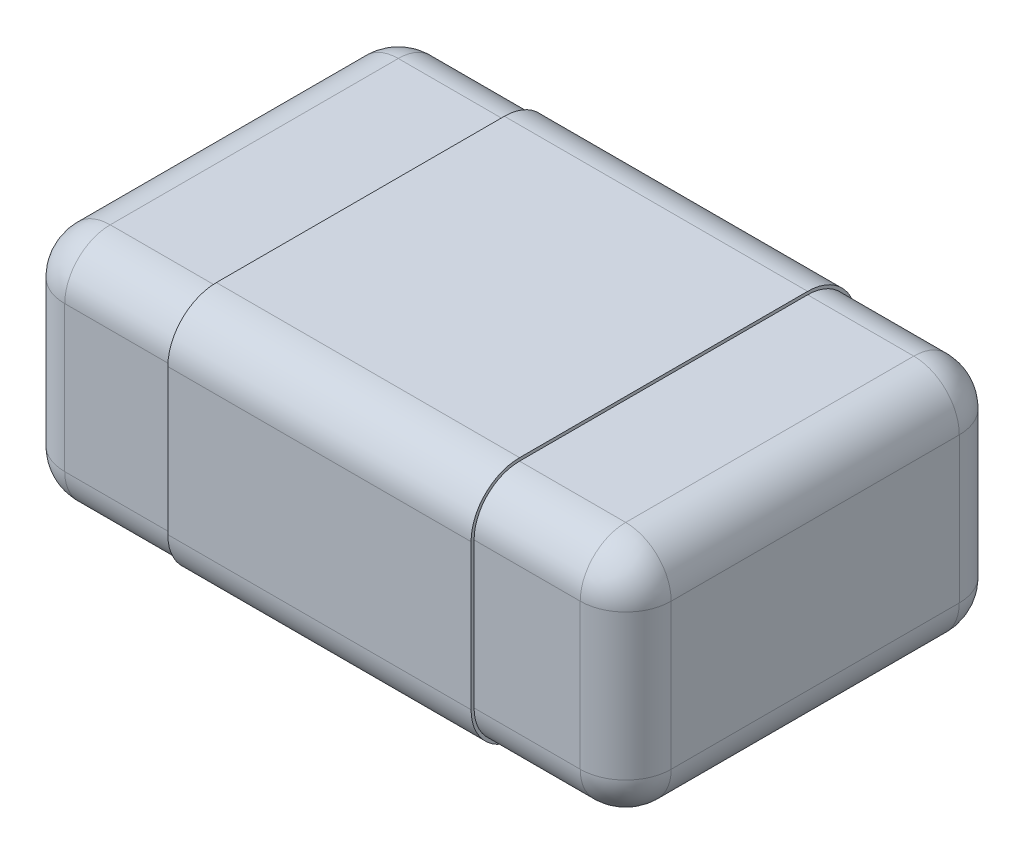
SolidWorks part; units mm, degrees
material "Aço inoxidável fundido"
ref_plane "Plano frontal" through (0, 0, 0) normal (0, 0, 1) x (1, 0, 0)
ref_plane "Plano superior" through (0, 0, 0) normal (0, 1, 0) x (1, 0, 0)
ref_plane "Plano direito" through (0, 0, 0) normal (1, 0, 0) x (0, 0, -1)
sketch "Esboço1" plane through (0, 0, 0) normal (0, 1, 0) x (1, 0, 0)
  line L0 (-1, -0.625) -> (1, -0.625)
  line L1 (1, -0.625) -> (1, 0.625)
  line L2 (1, 0.625) -> (-1, 0.625)
  line L3 (-1, 0.625) -> (-1, -0.625)
extrude "Ressalto-extrusão1" add sketch "Esboço1" against normal blind 0.78
fillet "Filete1" radius 0.15 12 edges at (0, -0.78, -0.625) (-1, -0.39, -0.625) (1, -0.39, -0.625) (0, 0, -0.625) (-1, -0.78, 0) (1, -0.78, 0) (0, -0.78, 0.625) (-1, 0, 0) (1, 0, 0) (-1, -0.39, 0.625) (1, -0.39, 0.625) (0, 0, 0.625)
sketch "Esboço4" plane through (0, 0, 0) normal (1, 0, 0) x (0, 0, -1)
  line L0 (0.625, -0.63) -> (0.625, -0.15) construction
  line L1 (0.625, -0.63) -> (0.625, -0.15)
  line L2 (0.475, -0.78) -> (-0.475, -0.78) construction
  line L3 (0.475, -0.78) -> (-0.475, -0.78)
  line L4 (0.475, 0) -> (-0.475, 0) construction
  line L5 (-0.625, -0.15) -> (-0.625, -0.63) construction
  line L6 (0.475, 0) -> (-0.475, 0)
  line L7 (-0.625, -0.15) -> (-0.625, -0.63)
  line L8 (0.635, -0.63) -> (0.635, -0.15)
  line L9 (0.475, 0.01) -> (-0.475, 0.01)
  line L10 (-0.635, -0.15) -> (-0.635, -0.63)
  line L11 (0.475, -0.79) -> (-0.475, -0.79)
  arc A5 (0.475, -0.78) -> (0.625, -0.63) centre (0.475, -0.63) ccw construction
  arc A6 (0.475, -0.78) -> (0.625, -0.63) centre (0.475, -0.63) ccw
  arc A7 (-0.475, 0) -> (-0.625, -0.15) centre (-0.475, -0.15) ccw construction
  arc A8 (-0.625, -0.63) -> (-0.475, -0.78) centre (-0.475, -0.63) ccw construction
  arc A9 (-0.475, 0) -> (-0.625, -0.15) centre (-0.475, -0.15) ccw
  arc A10 (-0.625, -0.63) -> (-0.475, -0.78) centre (-0.475, -0.63) ccw
  arc A11 (0.625, -0.15) -> (0.475, 0) centre (0.475, -0.15) ccw construction
  arc A12 (0.625, -0.15) -> (0.475, 0) centre (0.475, -0.15) ccw
  arc A13 (0.635, -0.15) -> (0.475, 0.01) centre (0.475, -0.15) ccw
  arc A14 (-0.475, 0.01) -> (-0.635, -0.15) centre (-0.475, -0.15) ccw
  arc A15 (-0.635, -0.63) -> (-0.475, -0.79) centre (-0.475, -0.63) ccw
  arc A16 (0.475, -0.79) -> (0.635, -0.63) centre (0.475, -0.63) ccw
  dimension "D1" = 0.01
extrude "Ressalto-extrusão4" add sketch "Esboço4" along normal blind 0.5 and the other way blind 0.5
